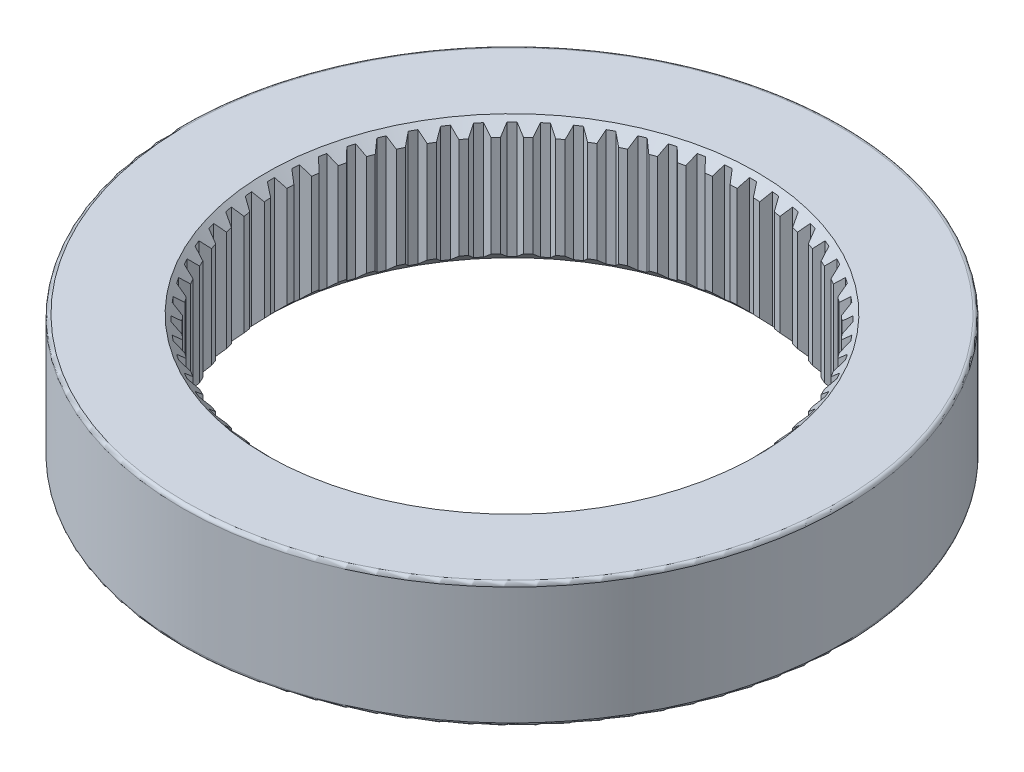
SolidWorks part; units mm, degrees
ref_plane "Front Plane" through (0, 0, 0) normal (0, 0, 1) x (1, 0, 0)
ref_plane "Top Plane" through (0, 0, 0) normal (0, 1, 0) x (1, 0, 0)
ref_plane "Right Plane" through (0, 0, 0) normal (1, 0, 0) x (0, 0, -1)
sketch "Sketch1" plane through (0, 0, 0) normal (0, 1, 0) x (1, 0, 0)
  circle A0 centre (0, 0) radius 35.56
  dimension "D1" = 71.12
extrude "Boss-Extrude1" add sketch "Sketch1" along normal blind 13.462 contours A0
sketch "Sketch2" plane through (0, 13.462, 0) normal (0, 1, 0) x (1, 0, 0)
  circle A0 centre (0, 0) radius 25.1841
  dimension "D1" = 50.3682
extrude "Cut-Extrude1" cut sketch "Sketch2" against normal blind 40.64
fillet "Fillet1" radius 0.381 1 edges at (0, 13.462, 35.56)
fillet "Fillet2" radius 0.381 1 edges at (0, 0, 35.56)
chamfer "Chamfer1" distance 1.2827 angle 45 1 edges at (0, 13.462, 25.1841)
chamfer "Chamfer2" distance 1.2827 angle 45 1 edges at (0, 0, 25.1841)
sketch "Sketch3" plane through (0, 13.462, 0) normal (0, 1, 0) x (1, 0, 0)
  line L2 (-26.0131, 0.385) -> (-25.1431, 0.8873)
  line L3 (-26.0131, -0.385) -> (-25.1431, -0.8873)
  line L5 (-25.9255, 2.1666) -> (-25.1089, 1.5815)
  line L6 (-25.8501, 2.9328) -> (-24.935, 3.3474)
  line L8 (-25.5883, 4.6973) -> (-24.833, 4.035)
  line L9 (-25.4381, 5.4525) -> (-24.4868, 5.7754)
  line L11 (-25.0047, 7.1828) -> (-24.318, 6.4496)
  line L12 (-24.7812, 7.9196) -> (-23.8028, 8.1477)
  line L14 (-24.1802, 9.5991) -> (-23.5687, 8.8021)
  line L15 (-23.8856, 10.3104) -> (-22.8896, 10.4415)
  line L17 (-23.1229, 11.923) -> (-22.5924, 11.0699)
  line L18 (-22.76, 12.602) -> (-21.7559, 12.6348)
  line L20 (-21.8429, 14.132) -> (-21.3986, 13.231)
  line L21 (-21.4152, 14.7722) -> (-20.4127, 14.7065)
  line L23 (-20.3526, 16.2049) -> (-19.9987, 15.2647)
  line L24 (-19.8641, 16.8001) -> (-18.873, 16.6364)
  line L26 (-18.6662, 18.1218) -> (-18.4062, 17.1514)
  line L27 (-18.1218, 18.6662) -> (-17.1514, 18.4062)
  line L29 (-16.8001, 19.8641) -> (-16.6364, 18.873)
  line L30 (-16.2049, 20.3526) -> (-15.2647, 19.9987)
  line L32 (-14.7722, 21.4152) -> (-14.7065, 20.4127)
  line L33 (-14.132, 21.8429) -> (-13.231, 21.3986)
  line L35 (-12.602, 22.76) -> (-12.6348, 21.7559)
  line L36 (-11.923, 23.1229) -> (-11.0699, 22.5924)
  line L38 (-10.3104, 23.8856) -> (-10.4415, 22.8896)
  line L39 (-9.5991, 24.1802) -> (-8.8021, 23.5687)
  line L41 (-7.9196, 24.7812) -> (-8.1477, 23.8028)
  line L42 (-7.1828, 25.0047) -> (-6.4496, 24.318)
  line L44 (-5.4525, 25.4381) -> (-5.7754, 24.4868)
  line L45 (-4.6973, 25.5883) -> (-4.035, 24.833)
  line L47 (-2.9328, 25.8501) -> (-3.3474, 24.935)
  line L48 (-2.1666, 25.9255) -> (-1.5815, 25.1089)
  line L50 (-0.385, 26.0131) -> (-0.8873, 25.1431)
  line L51 (0.385, 26.0131) -> (0.8873, 25.1431)
  line L53 (2.1666, 25.9255) -> (1.5815, 25.1089)
  line L54 (2.9328, 25.8501) -> (3.3474, 24.935)
  line L56 (4.6973, 25.5883) -> (4.035, 24.833)
  line L57 (5.4525, 25.4381) -> (5.7754, 24.4868)
  line L59 (7.1828, 25.0047) -> (6.4496, 24.318)
  line L60 (7.9196, 24.7812) -> (8.1477, 23.8028)
  line L62 (9.5991, 24.1802) -> (8.8021, 23.5687)
  line L63 (10.3104, 23.8856) -> (10.4415, 22.8896)
  line L65 (11.923, 23.1229) -> (11.0699, 22.5924)
  line L66 (12.602, 22.76) -> (12.6348, 21.7559)
  line L68 (14.132, 21.8429) -> (13.231, 21.3986)
  line L69 (14.7722, 21.4152) -> (14.7065, 20.4127)
  line L71 (16.2049, 20.3526) -> (15.2647, 19.9987)
  line L72 (16.8001, 19.8641) -> (16.6364, 18.873)
  line L74 (18.1218, 18.6662) -> (17.1514, 18.4062)
  line L75 (18.6662, 18.1218) -> (18.4062, 17.1514)
  line L77 (19.8641, 16.8001) -> (18.873, 16.6364)
  line L78 (20.3526, 16.2049) -> (19.9987, 15.2647)
  line L80 (21.4152, 14.7722) -> (20.4127, 14.7065)
  line L81 (21.8429, 14.132) -> (21.3986, 13.231)
  line L83 (22.76, 12.602) -> (21.7559, 12.6348)
  line L84 (23.1229, 11.923) -> (22.5924, 11.0699)
  line L86 (23.8856, 10.3104) -> (22.8896, 10.4415)
  line L87 (24.1802, 9.5991) -> (23.5687, 8.8021)
  line L89 (24.7812, 7.9196) -> (23.8028, 8.1477)
  line L90 (25.0047, 7.1828) -> (24.318, 6.4496)
  line L92 (25.4381, 5.4525) -> (24.4868, 5.7754)
  line L93 (25.5883, 4.6973) -> (24.833, 4.035)
  line L95 (25.8501, 2.9328) -> (24.935, 3.3474)
  line L96 (25.9255, 2.1666) -> (25.1089, 1.5815)
  line L98 (26.0131, 0.385) -> (25.1431, 0.8873)
  line L99 (26.0131, -0.385) -> (25.1431, -0.8873)
  line L101 (25.9255, -2.1666) -> (25.1089, -1.5815)
  line L102 (25.8501, -2.9328) -> (24.935, -3.3474)
  line L104 (25.5883, -4.6973) -> (24.833, -4.035)
  line L105 (25.4381, -5.4525) -> (24.4868, -5.7754)
  line L107 (25.0047, -7.1828) -> (24.318, -6.4496)
  line L108 (24.7812, -7.9196) -> (23.8028, -8.1477)
  line L110 (24.1802, -9.5991) -> (23.5687, -8.8021)
  line L111 (23.8856, -10.3104) -> (22.8896, -10.4415)
  line L113 (23.1229, -11.923) -> (22.5924, -11.0699)
  line L114 (22.76, -12.602) -> (21.7559, -12.6348)
  line L116 (21.8429, -14.132) -> (21.3986, -13.231)
  line L117 (21.4152, -14.7722) -> (20.4127, -14.7065)
  line L119 (20.3526, -16.2049) -> (19.9987, -15.2647)
  line L120 (19.8641, -16.8001) -> (18.873, -16.6364)
  line L122 (18.6662, -18.1218) -> (18.4062, -17.1514)
  line L123 (18.1218, -18.6662) -> (17.1514, -18.4062)
  line L125 (16.8001, -19.8641) -> (16.6364, -18.873)
  line L126 (16.2049, -20.3526) -> (15.2647, -19.9987)
  line L128 (14.7722, -21.4152) -> (14.7065, -20.4127)
  line L129 (14.132, -21.8429) -> (13.231, -21.3986)
  line L131 (12.602, -22.76) -> (12.6348, -21.7559)
  line L132 (11.923, -23.1229) -> (11.0699, -22.5924)
  line L134 (10.3104, -23.8856) -> (10.4415, -22.8896)
  line L135 (9.5991, -24.1802) -> (8.8021, -23.5687)
  line L137 (7.9196, -24.7812) -> (8.1477, -23.8028)
  line L138 (7.1828, -25.0047) -> (6.4496, -24.318)
  line L140 (5.4525, -25.4381) -> (5.7754, -24.4868)
  line L141 (4.6973, -25.5883) -> (4.035, -24.833)
  line L143 (2.9328, -25.8501) -> (3.3474, -24.935)
  line L144 (2.1666, -25.9255) -> (1.5815, -25.1089)
  line L146 (0.385, -26.0131) -> (0.8873, -25.1431)
  line L147 (-0.385, -26.0131) -> (-0.8873, -25.1431)
  line L149 (-2.1666, -25.9255) -> (-1.5815, -25.1089)
  line L150 (-2.9328, -25.8501) -> (-3.3474, -24.935)
  line L152 (-4.6973, -25.5883) -> (-4.035, -24.833)
  line L153 (-5.4525, -25.4381) -> (-5.7754, -24.4868)
  line L155 (-7.1828, -25.0047) -> (-6.4496, -24.318)
  line L156 (-7.9196, -24.7812) -> (-8.1477, -23.8028)
  line L158 (-9.5991, -24.1802) -> (-8.8021, -23.5687)
  line L159 (-10.3104, -23.8856) -> (-10.4415, -22.8896)
  line L161 (-11.923, -23.1229) -> (-11.0699, -22.5924)
  line L162 (-12.602, -22.76) -> (-12.6348, -21.7559)
  line L164 (-14.132, -21.8429) -> (-13.231, -21.3986)
  line L165 (-14.7722, -21.4152) -> (-14.7065, -20.4127)
  line L167 (-16.2049, -20.3526) -> (-15.2647, -19.9987)
  line L168 (-16.8001, -19.8641) -> (-16.6364, -18.873)
  line L170 (-18.1218, -18.6662) -> (-17.1514, -18.4062)
  line L171 (-18.6662, -18.1218) -> (-18.4062, -17.1514)
  line L173 (-19.8641, -16.8001) -> (-18.873, -16.6364)
  line L174 (-20.3526, -16.2049) -> (-19.9987, -15.2647)
  line L176 (-21.4152, -14.7722) -> (-20.4127, -14.7065)
  line L177 (-21.8429, -14.132) -> (-21.3986, -13.231)
  line L179 (-22.76, -12.602) -> (-21.7559, -12.6348)
  line L180 (-23.1229, -11.923) -> (-22.5924, -11.0699)
  line L182 (-23.8856, -10.3104) -> (-22.8896, -10.4415)
  line L183 (-24.1802, -9.5991) -> (-23.5687, -8.8021)
  line L185 (-24.7812, -7.9196) -> (-23.8028, -8.1477)
  line L186 (-25.0047, -7.1828) -> (-24.318, -6.4496)
  line L188 (-25.4381, -5.4525) -> (-24.4868, -5.7754)
  line L189 (-25.5883, -4.6973) -> (-24.833, -4.035)
  line L191 (-25.8501, -2.9328) -> (-24.935, -3.3474)
  line L192 (-25.9255, -2.1666) -> (-25.1089, -1.5815)
  arc A1 (-26.0131, 0.385) -> (-26.0131, -0.385) centre (0, 0) ccw
  arc A2 (-25.1431, 0.8873) -> (-25.1431, -0.8873) centre (0, 0) ccw
  arc A3 (-24.935, 3.3474) -> (-25.1089, 1.5815) centre (0, 0) ccw
  arc A4 (-25.8501, 2.9328) -> (-25.9255, 2.1666) centre (0, 0) ccw
  arc A5 (-24.4868, 5.7754) -> (-24.833, 4.035) centre (0, 0) ccw
  arc A6 (-25.4381, 5.4525) -> (-25.5883, 4.6973) centre (0, 0) ccw
  arc A7 (-23.8028, 8.1477) -> (-24.318, 6.4496) centre (0, 0) ccw
  arc A8 (-24.7812, 7.9196) -> (-25.0047, 7.1828) centre (0, 0) ccw
  arc A9 (-22.8896, 10.4415) -> (-23.5687, 8.8021) centre (0, 0) ccw
  arc A10 (-23.8856, 10.3104) -> (-24.1802, 9.5991) centre (0, 0) ccw
  arc A11 (-21.7559, 12.6348) -> (-22.5924, 11.0699) centre (0, 0) ccw
  arc A12 (-22.76, 12.602) -> (-23.1229, 11.923) centre (0, 0) ccw
  arc A13 (-20.4127, 14.7065) -> (-21.3986, 13.231) centre (0, 0) ccw
  arc A14 (-21.4152, 14.7722) -> (-21.8429, 14.132) centre (0, 0) ccw
  arc A15 (-18.873, 16.6364) -> (-19.9987, 15.2647) centre (0, 0) ccw
  arc A16 (-19.8641, 16.8001) -> (-20.3526, 16.2049) centre (0, 0) ccw
  arc A17 (-17.1514, 18.4062) -> (-18.4062, 17.1514) centre (0, 0) ccw
  arc A18 (-18.1218, 18.6662) -> (-18.6662, 18.1218) centre (0, 0) ccw
  arc A19 (-15.2647, 19.9987) -> (-16.6364, 18.873) centre (0, 0) ccw
  arc A20 (-16.2049, 20.3526) -> (-16.8001, 19.8641) centre (0, 0) ccw
  arc A21 (-13.231, 21.3986) -> (-14.7065, 20.4127) centre (0, 0) ccw
  arc A22 (-14.132, 21.8429) -> (-14.7722, 21.4152) centre (0, 0) ccw
  arc A23 (-11.0699, 22.5924) -> (-12.6348, 21.7559) centre (0, 0) ccw
  arc A24 (-11.923, 23.1229) -> (-12.602, 22.76) centre (0, 0) ccw
  arc A25 (-8.8021, 23.5687) -> (-10.4415, 22.8896) centre (0, 0) ccw
  arc A26 (-9.5991, 24.1802) -> (-10.3104, 23.8856) centre (0, 0) ccw
  arc A27 (-6.4496, 24.318) -> (-8.1477, 23.8028) centre (0, 0) ccw
  arc A28 (-7.1828, 25.0047) -> (-7.9196, 24.7812) centre (0, 0) ccw
  arc A29 (-4.035, 24.833) -> (-5.7754, 24.4868) centre (0, 0) ccw
  arc A30 (-4.6973, 25.5883) -> (-5.4525, 25.4381) centre (0, 0) ccw
  arc A31 (-1.5815, 25.1089) -> (-3.3474, 24.935) centre (0, 0) ccw
  arc A32 (-2.1666, 25.9255) -> (-2.9328, 25.8501) centre (0, 0) ccw
  arc A33 (0.8873, 25.1431) -> (-0.8873, 25.1431) centre (0, 0) ccw
  arc A34 (0.385, 26.0131) -> (-0.385, 26.0131) centre (0, 0) ccw
  arc A35 (3.3474, 24.935) -> (1.5815, 25.1089) centre (0, 0) ccw
  arc A36 (2.9328, 25.8501) -> (2.1666, 25.9255) centre (0, 0) ccw
  arc A37 (5.7754, 24.4868) -> (4.035, 24.833) centre (0, 0) ccw
  arc A38 (5.4525, 25.4381) -> (4.6973, 25.5883) centre (0, 0) ccw
  arc A39 (8.1477, 23.8028) -> (6.4496, 24.318) centre (0, 0) ccw
  arc A40 (7.9196, 24.7812) -> (7.1828, 25.0047) centre (0, 0) ccw
  arc A41 (10.4415, 22.8896) -> (8.8021, 23.5687) centre (0, 0) ccw
  arc A42 (10.3104, 23.8856) -> (9.5991, 24.1802) centre (0, 0) ccw
  arc A43 (12.6348, 21.7559) -> (11.0699, 22.5924) centre (0, 0) ccw
  arc A44 (12.602, 22.76) -> (11.923, 23.1229) centre (0, 0) ccw
  arc A45 (14.7065, 20.4127) -> (13.231, 21.3986) centre (0, 0) ccw
  arc A46 (14.7722, 21.4152) -> (14.132, 21.8429) centre (0, 0) ccw
  arc A47 (16.6364, 18.873) -> (15.2647, 19.9987) centre (0, 0) ccw
  arc A48 (16.8001, 19.8641) -> (16.2049, 20.3526) centre (0, 0) ccw
  arc A49 (18.4062, 17.1514) -> (17.1514, 18.4062) centre (0, 0) ccw
  arc A50 (18.6662, 18.1218) -> (18.1218, 18.6662) centre (0, 0) ccw
  arc A51 (19.9987, 15.2647) -> (18.873, 16.6364) centre (0, 0) ccw
  arc A52 (20.3526, 16.2049) -> (19.8641, 16.8001) centre (0, 0) ccw
  arc A53 (21.3986, 13.231) -> (20.4127, 14.7065) centre (0, 0) ccw
  arc A54 (21.8429, 14.132) -> (21.4152, 14.7722) centre (0, 0) ccw
  arc A55 (22.5924, 11.0699) -> (21.7559, 12.6348) centre (0, 0) ccw
  arc A56 (23.1229, 11.923) -> (22.76, 12.602) centre (0, 0) ccw
  arc A57 (23.5687, 8.8021) -> (22.8896, 10.4415) centre (0, 0) ccw
  arc A58 (24.1802, 9.5991) -> (23.8856, 10.3104) centre (0, 0) ccw
  arc A59 (24.318, 6.4496) -> (23.8028, 8.1477) centre (0, 0) ccw
  arc A60 (25.0047, 7.1828) -> (24.7812, 7.9196) centre (0, 0) ccw
  arc A61 (24.833, 4.035) -> (24.4868, 5.7754) centre (0, 0) ccw
  arc A62 (25.5883, 4.6973) -> (25.4381, 5.4525) centre (0, 0) ccw
  arc A63 (25.1089, 1.5815) -> (24.935, 3.3474) centre (0, 0) ccw
  arc A64 (25.9255, 2.1666) -> (25.8501, 2.9328) centre (0, 0) ccw
  arc A65 (25.1431, -0.8873) -> (25.1431, 0.8873) centre (0, 0) ccw
  arc A66 (26.0131, -0.385) -> (26.0131, 0.385) centre (0, 0) ccw
  arc A67 (24.935, -3.3474) -> (25.1089, -1.5815) centre (0, 0) ccw
  arc A68 (25.8501, -2.9328) -> (25.9255, -2.1666) centre (0, 0) ccw
  arc A69 (24.4868, -5.7754) -> (24.833, -4.035) centre (0, 0) ccw
  arc A70 (25.4381, -5.4525) -> (25.5883, -4.6973) centre (0, 0) ccw
  arc A71 (23.8028, -8.1477) -> (24.318, -6.4496) centre (0, 0) ccw
  arc A72 (24.7812, -7.9196) -> (25.0047, -7.1828) centre (0, 0) ccw
  arc A73 (22.8896, -10.4415) -> (23.5687, -8.8021) centre (0, 0) ccw
  arc A74 (23.8856, -10.3104) -> (24.1802, -9.5991) centre (0, 0) ccw
  arc A75 (21.7559, -12.6348) -> (22.5924, -11.0699) centre (0, 0) ccw
  arc A76 (22.76, -12.602) -> (23.1229, -11.923) centre (0, 0) ccw
  arc A77 (20.4127, -14.7065) -> (21.3986, -13.231) centre (0, 0) ccw
  arc A78 (21.4152, -14.7722) -> (21.8429, -14.132) centre (0, 0) ccw
  arc A79 (18.873, -16.6364) -> (19.9987, -15.2647) centre (0, 0) ccw
  arc A80 (19.8641, -16.8001) -> (20.3526, -16.2049) centre (0, 0) ccw
  arc A81 (17.1514, -18.4062) -> (18.4062, -17.1514) centre (0, 0) ccw
  arc A82 (18.1218, -18.6662) -> (18.6662, -18.1218) centre (0, 0) ccw
  arc A83 (15.2647, -19.9987) -> (16.6364, -18.873) centre (0, 0) ccw
  arc A84 (16.2049, -20.3526) -> (16.8001, -19.8641) centre (0, 0) ccw
  arc A85 (13.231, -21.3986) -> (14.7065, -20.4127) centre (0, 0) ccw
  arc A86 (14.132, -21.8429) -> (14.7722, -21.4152) centre (0, 0) ccw
  arc A87 (11.0699, -22.5924) -> (12.6348, -21.7559) centre (0, 0) ccw
  arc A88 (11.923, -23.1229) -> (12.602, -22.76) centre (0, 0) ccw
  arc A89 (8.8021, -23.5687) -> (10.4415, -22.8896) centre (0, 0) ccw
  arc A90 (9.5991, -24.1802) -> (10.3104, -23.8856) centre (0, 0) ccw
  arc A91 (6.4496, -24.318) -> (8.1477, -23.8028) centre (0, 0) ccw
  arc A92 (7.1828, -25.0047) -> (7.9196, -24.7812) centre (0, 0) ccw
  arc A93 (4.035, -24.833) -> (5.7754, -24.4868) centre (0, 0) ccw
  arc A94 (4.6973, -25.5883) -> (5.4525, -25.4381) centre (0, 0) ccw
  arc A95 (1.5815, -25.1089) -> (3.3474, -24.935) centre (0, 0) ccw
  arc A96 (2.1666, -25.9255) -> (2.9328, -25.8501) centre (0, 0) ccw
  arc A97 (-0.8873, -25.1431) -> (0.8873, -25.1431) centre (0, 0) ccw
  arc A98 (-0.385, -26.0131) -> (0.385, -26.0131) centre (0, 0) ccw
  arc A99 (-3.3474, -24.935) -> (-1.5815, -25.1089) centre (0, 0) ccw
  arc A100 (-2.9328, -25.8501) -> (-2.1666, -25.9255) centre (0, 0) ccw
  arc A101 (-5.7754, -24.4868) -> (-4.035, -24.833) centre (0, 0) ccw
  arc A102 (-5.4525, -25.4381) -> (-4.6973, -25.5883) centre (0, 0) ccw
  arc A103 (-8.1477, -23.8028) -> (-6.4496, -24.318) centre (0, 0) ccw
  arc A104 (-7.9196, -24.7812) -> (-7.1828, -25.0047) centre (0, 0) ccw
  arc A105 (-10.4415, -22.8896) -> (-8.8021, -23.5687) centre (0, 0) ccw
  arc A106 (-10.3104, -23.8856) -> (-9.5991, -24.1802) centre (0, 0) ccw
  arc A107 (-12.6348, -21.7559) -> (-11.0699, -22.5924) centre (0, 0) ccw
  arc A108 (-12.602, -22.76) -> (-11.923, -23.1229) centre (0, 0) ccw
  arc A109 (-14.7065, -20.4127) -> (-13.231, -21.3986) centre (0, 0) ccw
  arc A110 (-14.7722, -21.4152) -> (-14.132, -21.8429) centre (0, 0) ccw
  arc A111 (-16.6364, -18.873) -> (-15.2647, -19.9987) centre (0, 0) ccw
  arc A112 (-16.8001, -19.8641) -> (-16.2049, -20.3526) centre (0, 0) ccw
  arc A113 (-18.4062, -17.1514) -> (-17.1514, -18.4062) centre (0, 0) ccw
  arc A114 (-18.6662, -18.1218) -> (-18.1218, -18.6662) centre (0, 0) ccw
  arc A115 (-19.9987, -15.2647) -> (-18.873, -16.6364) centre (0, 0) ccw
  arc A116 (-20.3526, -16.2049) -> (-19.8641, -16.8001) centre (0, 0) ccw
  arc A117 (-21.3986, -13.231) -> (-20.4127, -14.7065) centre (0, 0) ccw
  arc A118 (-21.8429, -14.132) -> (-21.4152, -14.7722) centre (0, 0) ccw
  arc A119 (-22.5924, -11.0699) -> (-21.7559, -12.6348) centre (0, 0) ccw
  arc A120 (-23.1229, -11.923) -> (-22.76, -12.602) centre (0, 0) ccw
  arc A121 (-23.5687, -8.8021) -> (-22.8896, -10.4415) centre (0, 0) ccw
  arc A122 (-24.1802, -9.5991) -> (-23.8856, -10.3104) centre (0, 0) ccw
  arc A123 (-24.318, -6.4496) -> (-23.8028, -8.1477) centre (0, 0) ccw
  arc A124 (-25.0047, -7.1828) -> (-24.7812, -7.9196) centre (0, 0) ccw
  arc A125 (-24.833, -4.035) -> (-24.4868, -5.7754) centre (0, 0) ccw
  arc A126 (-25.5883, -4.6973) -> (-25.4381, -5.4525) centre (0, 0) ccw
  arc A127 (-25.1089, -1.5815) -> (-24.935, -3.3474) centre (0, 0) ccw
  arc A128 (-25.9255, -2.1666) -> (-25.8501, -2.9328) centre (0, 0) ccw
  point P329 (0, 0)
  dimension "D2" = 52.0318
  dimension "D3" = 50.3174
  dimension "D6" = 64
extrude "Cut-Extrude2" cut sketch "Sketch3" against normal up to surface (13.462 mm away) up to face at (0, 0, 26.4668)
